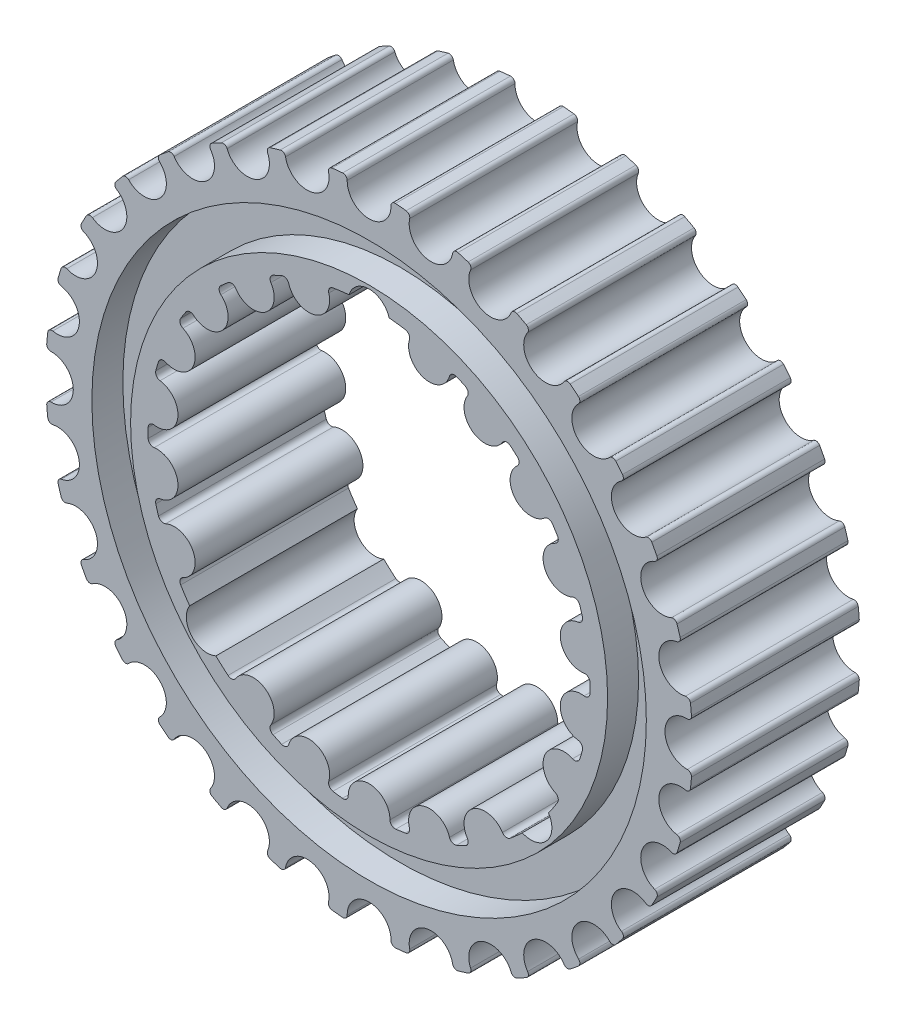
SolidWorks part; units mm, degrees
material "6061 Alloy"
ref_plane "Front Plane" through (0, 0, 0) normal (0, 0, 1) x (1, 0, 0)
ref_plane "Top Plane" through (0, 0, 0) normal (0, 1, 0) x (1, 0, 0)
ref_plane "Right Plane" through (0, 0, 0) normal (1, 0, 0) x (0, 0, -1)
sketch "Sketch1" plane through (0, 0, 0) normal (0, 0, 1) x (1, 0, 0)
  line L3 (3.27, 26.8516) -> (0, 0) construction
  line L4 (-3.8496, 26.7747) -> (0, 0) construction
  line L5 (3.8496, 26.7747) -> (0, 0) construction
  line L6 (-3.8677, 26.9004) -> (-3.9864, 27.7262)
  line L7 (3.8677, 26.9004) -> (3.9864, 27.7262)
  line L8 (-2.6956, 26.3433) -> (-2.6997, 31.2639) construction
  line L9 (2.6956, 26.3433) -> (2.6997, 31.195) construction
  circle A1 centre (0, 0) radius 28.0113 construction
  circle A2 centre (0, 0) radius 26.4809 construction
  arc A3 (-2.6956, 26.3433) -> (2.6956, 26.3433) centre (0, 26.3456) ccw construction
  arc A4 (2.6956, 26.3433) -> (3.27, 26.8516) centre (3.2081, 26.3429) cw construction
  arc A5 (-2.6956, 26.3433) -> (-3.27, 26.8516) centre (-3.2081, 26.3429) ccw construction
  arc A6 (-3.27, 26.8516) -> (-3.8496, 26.7747) centre (0, 0) ccw construction
  arc A7 (3.27, 26.8516) -> (3.8496, 26.7747) centre (0, 0) cw construction
  arc A8 (-3.9864, 27.7262) -> (3.9864, 27.7262) centre (0, 0) cw
  circle A9 centre (0, 0) radius 23.65 construction
  arc A10 (3.2854, 26.9777) -> (3.8677, 26.9004) centre (0, 0) cw
  arc A11 (2.5686, 26.3434) -> (3.2854, 26.9777) centre (3.2081, 26.3429) cw
  arc A12 (-2.5686, 26.3434) -> (2.5686, 26.3434) centre (0, 26.3456) ccw
  arc A13 (-2.5686, 26.3434) -> (-3.2854, 26.9777) centre (-3.2081, 26.3429) ccw
  arc A14 (-3.2854, 26.9777) -> (-3.8677, 26.9004) centre (0, 0) ccw
  point P1 (-3.9864, 27.7262)
  point P8 (0, 28.0113)
  point P9 (-2.6956, 26.3433)
  point P10 (2.6956, 26.3433)
  point P21 (-3.3657, 23.4093)
  point P22 (0, 23.65)
  dimension "D4" = 5.3912
  dimension "D1" = 47.3
  dimension "D8" = 56.0226
  dimension "D6" = 16.364
  dimension "D9" = 3.4
  dimension "D10" = 27.05
  dimension "D2" = 0.9613
  dimension "D5" = 0.096
  dimension "D3" = 0.127
extrude "Boss-Extrude1" add sketch "Sketch1" along normal mid plane 20.6375
ref_axis "Axis1" through (0, 0, 11.3506) along (0, 0, -1)
pattern_circular "CirPattern2" count 22 over 360 about axis through (0, 0, 0) along (0, 0, 1) of "Boss-Extrude1"
sketch "Sketch2" plane through (0, 0, 0) normal (0, 0, 1) x (1, 0, 0)
  circle A0 centre (0, 0) radius 13
  dimension "D1" = 26
extrude "Boss-Extrude2" [suppressed] add sketch "Sketch2" along normal mid plane 20.6375 separate body
sketch "Sketch4" plane through (0, 0, 0) normal (0, 0, 1) x (1, 0, 0)
  line L0 (-3.8994, 39.5908) -> (-2.7456, 27.8764)
  line L1 (2.7456, 27.8764) -> (3.8994, 39.5908)
  line L2 (0, 40.7437) -> (0, 36.3824) construction
  line L3 (-3.8496, 26.7747) -> (-3.3657, 23.4093) construction
  circle A0 centre (0, 0) radius 40.7437 construction
  arc A1 (-2.6951, 39.129) -> (2.6951, 39.129) centre (0, 39.078) ccw
  arc A2 (-2.6956, 26.3433) -> (2.6956, 26.3433) centre (0, 26.3456) ccw construction
  circle A3 centre (0, 0) radius 28.0113 construction
  arc A4 (2.7456, 27.8764) -> (-2.7456, 27.8764) centre (0, 0) ccw
  arc A5 (-2.6951, 39.129) -> (-3.2493, 39.6495) centre (-3.2075, 39.1387) ccw
  arc A6 (-3.8994, 39.5908) -> (-3.2493, 39.6495) centre (0, 0) cw
  arc A7 (0, 36.3824) -> (-3.5661, 36.2072) centre (0, 0) ccw construction
  arc A8 (3.8994, 39.5908) -> (3.2493, 39.6495) centre (0, 0) ccw
  arc A9 (3.2493, 39.6495) -> (2.6951, 39.129) centre (3.2075, 39.1387) ccw
  arc A10 (-2.6956, 26.3433) -> (-3.27, 26.8516) centre (-3.2081, 26.3429) ccw construction
  point P26 (0, 36.3824)
  point P47 (-3.9936, 40.5475)
  dimension "D2" = 11.25
  dimension "D4" = 3.4
  dimension "D3" = 3.4
  dimension "D5" = 0.9613
  dimension "D6" = 0.9613
extrude "Boss-Extrude3" add sketch "Sketch4" against normal up to surface (10.3187 mm away) and the other way up to surface (10.3187 mm away) up to face at (-28.0113, 0, -10.3187) other way up to face at (-28.0113, 0, 10.3187)
pattern_circular "CirPattern3" count 32 over 360 about axis through (0, 0, 0) along (0, 0, 1) of "Boss-Extrude3"
sketch "Sketch7" plane through (0, 0, 10.3187) normal (0, 0, 1) x (1, 0, 0)
  line L0 (0, 27.05) -> (0, 36.3824) construction
  line L1 (0, 34.0975) -> (0, 29.335) construction
  circle A0 centre (0, 0) radius 34.0975
  circle A1 centre (0, 0) radius 29.335
  arc A3 (-3.27, 26.8516) -> (-3.8496, 26.7747) centre (0, 0) ccw construction
  point P4 (0, 34.0975)
  point P5 (0, 29.335)
  point P6 (0, 27.05)
  point P11 (0, 31.7162)
  dimension "D1" = 4.7625
extrude "Cut-Extrude2" cut sketch "Sketch7" against normal blind 3.81
pattern_circular "CirPattern6" [suppressed] count 8 over 360 about axis through (0, 0, 11.3506) along (0, 0, -1)
sketch "Sketch11" plane through (0, 0, 10.3187) normal (0, 0, 1) x (1, 0, 0)
  arc A2 (3.2854, 26.9777) -> (2.5686, 26.3434) centre (3.2081, 26.3429) ccw construction
  arc A3 (-2.5686, 26.3434) -> (2.5686, 26.3434) centre (0, 26.3456) ccw construction
  arc A4 (-2.5686, 26.3434) -> (-3.2854, 26.9777) centre (-3.2081, 26.3429) ccw construction
  arc A9 (3.2854, 26.9777) -> (2.5686, 26.3434) centre (3.2081, 26.3429) ccw
  arc A13 (-2.4658, 27.0649) -> (2.4658, 27.0649) centre (0, 26.3456) cw
  arc A14 (-2.4658, 27.0649) -> (-3.2854, 26.9777) centre (0, 0) ccw
  arc A15 (-2.5686, 26.3434) -> (2.5686, 26.3434) centre (0, 26.3456) ccw
  arc A16 (-2.5686, 26.3434) -> (-3.2854, 26.9777) centre (-3.2081, 26.3429) ccw
  arc A17 (-3.2854, 26.9777) -> (-4.4482, 26.8105) centre (0, 0) ccw construction
  arc A18 (3.2854, 26.9777) -> (2.4658, 27.0649) centre (0, 0) ccw
  arc A19 (4.4482, 26.8105) -> (3.2854, 26.9777) centre (0, 0) ccw construction
extrude "Cut-Extrude3" cut sketch "Sketch11" against normal through all both and the other way through all
pattern_circular "CirPattern9" count 11 over 360 about axis through (0, 0, 11.3506) along (0, 0, -1) skipping 1, 2, 3, 5, 6, 8, 9, 10 of "Cut-Extrude3"
equation "\"pitch\"=0.314961"
equation "\"D6@Sketch1\"=360/22"
equation "\"D8@Sketch1\"=\"pitch\"*22/pi"
equation "\"D1@Sketch4\" = \"pitch\" * \"teeth\" / pi"
equation "\"teeth\"= 32"
equation "\"D2@Sketch4\"=360/\"teeth\""
equation "\"D1@CirPattern3\"=\"teeth\""
